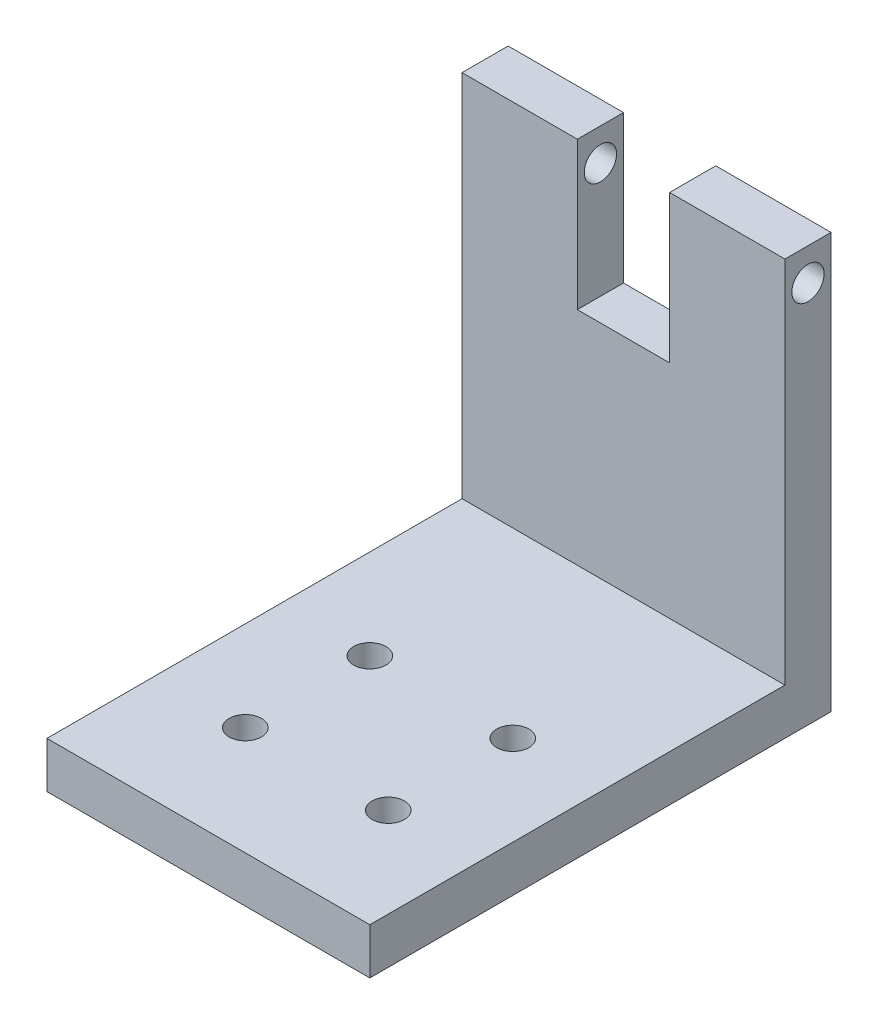
SolidWorks part; units mm, degrees
ref_plane "Front Plane" through (0, 0, 0) normal (0, 0, 1) x (1, 0, 0)
ref_plane "Top Plane" through (0, 0, 0) normal (0, 1, 0) x (1, 0, 0)
ref_plane "Right Plane" through (0, 0, 0) normal (1, 0, 0) x (0, 0, -1)
sketch "Sketch1" plane through (0, 0, 0) normal (0, 1, 0) x (1, 0, 0)
  line L1 (0, 0) -> (35, 0)
  line L2 (0, 0) -> (0, 50)
  line L3 (0, 50) -> (35, 50)
  line L4 (35, 0) -> (35, 50)
  dimension "D1" = 50
  dimension "D2" = 35
extrude "Boss-Extrude1" add sketch "Sketch1" along normal blind 5
sketch "Sketch2" plane through (0, 5, 0) normal (0, 1, 0) x (1, 0, 0)
  line L0 (17.5, 0) -> (17.5, 50) construction
  line L1 (0, 0) -> (35, 0) construction
  line L2 (35, 50) -> (0, 50) construction
  line L4 (0, 50) -> (0, 0) construction
  circle A0 centre (9.75, 11.75) radius 1.75
  circle A1 centre (9.75, 25.25) radius 1.75
  circle A2 centre (25.25, 11.75) radius 1.75
  circle A3 centre (25.25, 25.25) radius 1.75
  point P12 (0, 0)
  dimension "D1" = 10
  dimension "D3" = 3.5
  dimension "D4" = 10
  dimension "D2" = 8
extrude "Cut-Extrude1" cut sketch "Sketch2" against normal through all
sketch "Sketch3" plane through (0, 5, 0) normal (0, 1, 0) x (1, 0, 0)
  line L0 (35, 0) -> (35, 50) construction
  line L1 (0, 50) -> (12.5, 50)
  line L2 (0, 50) -> (0, 45)
  line L3 (0, 45) -> (12.5, 45)
  line L4 (35, 50) -> (35, 45)
  line L5 (12.5, 50) -> (12.5, 45)
  line L6 (22.5, 45) -> (22.5, 50)
  line L7 (22.5, 50) -> (35, 50)
  line L8 (22.5, 45) -> (35, 45)
  dimension "D1" = 5
  dimension "D2" = 10
extrude "Boss-Extrude2" add sketch "Sketch3" along normal blind 40
sketch "Sketch4" plane through (0, 5, 0) normal (0, 1, 0) x (1, 0, 0)
  line L1 (12.5, 50) -> (22.5, 50)
  line L2 (12.5, 50) -> (12.5, 45)
  line L3 (12.5, 45) -> (22.5, 45)
  line L4 (22.5, 50) -> (22.5, 45)
extrude "Boss-Extrude3" add sketch "Sketch4" along normal blind 24
sketch "Sketch5" plane through (0, 0, 0) normal (-1, 0, 0) x (0, 0, 1)
  line L0 (-50, 45) -> (-45, 45) construction
  circle A0 centre (-47.5, 41.5) radius 1.75
  point P2 (0, 0)
  point P5 (-47.5, 45)
  dimension "D1" = 3.5
  dimension "D2" = 3.5
extrude "Cut-Extrude2" cut sketch "Sketch5" against normal through all
